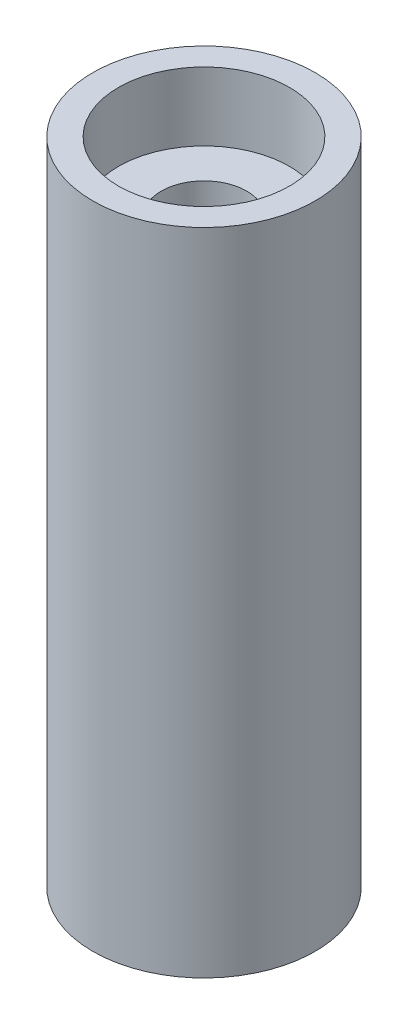
SolidWorks part; units mm, degrees
material "6061 合金"
ref_plane "前视基准面" through (0, 0, 0) normal (0, 0, 1) x (1, 0, 0)
ref_plane "上视基准面" through (0, 0, 0) normal (0, 1, 0) x (1, 0, 0)
ref_plane "右视基准面" through (0, 0, 0) normal (1, 0, 0) x (0, 0, -1)
sketch "草图1" plane through (0, 0, 0) normal (0, 1, 0) x (1, 0, 0)
  circle A0 centre (0, 0) radius 6.5
  circle A1 centre (0, 0) radius 2.5
  dimension "D1" = 13
  dimension "D2" = 5
extrude "凸台-拉伸2" add sketch "草图1" along normal mid plane 38
sketch "草图2" plane through (0, 19, 0) normal (0, 1, 0) x (1, 0, 0)
  circle A0 centre (0, 0) radius 5
  dimension "D1" = 10
extrude "切除-拉伸1" cut sketch "草图2" against normal blind 4
mirror "镜向1" about plane through (0, 0, 0) normal (0, 1, 0) of "切除-拉伸1"
